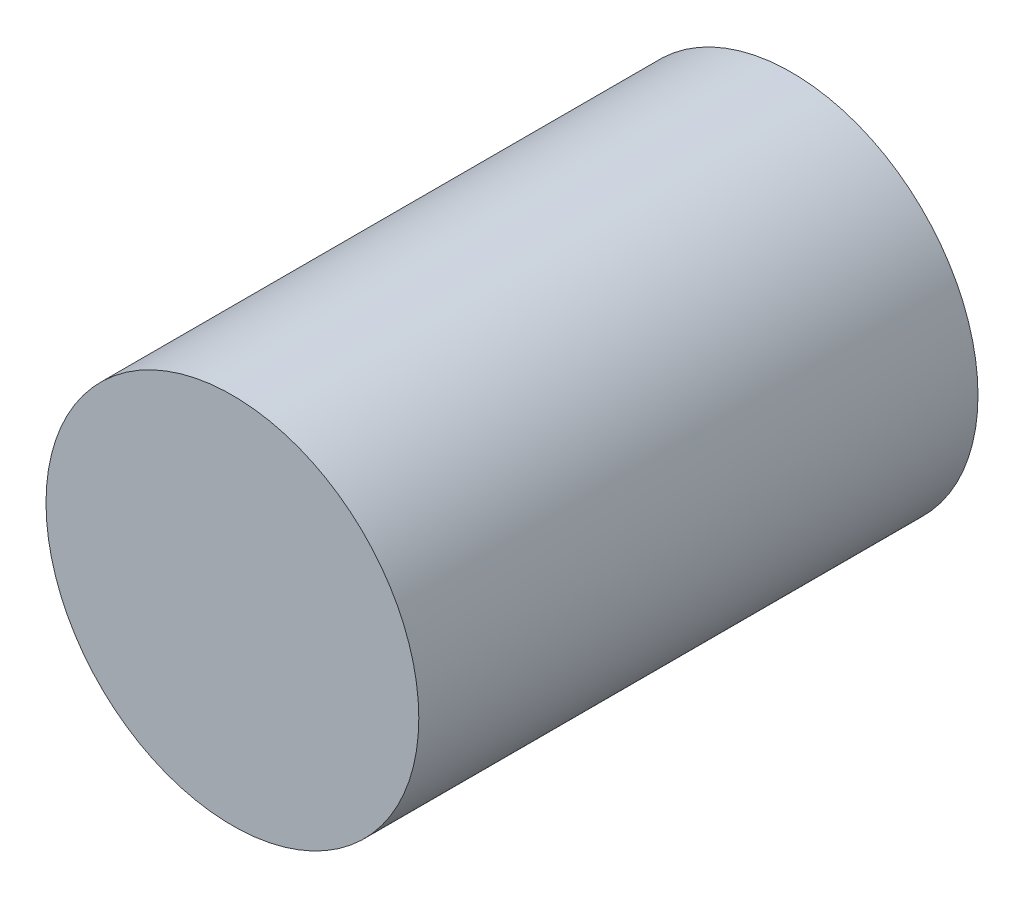
SolidWorks part; units mm, degrees
ref_plane "Front Plane" through (0, 0, 0) normal (0, 0, 1) x (1, 0, 0)
ref_plane "Top Plane" through (0, 0, 0) normal (0, 1, 0) x (1, 0, 0)
ref_plane "Right Plane" through (0, 0, 0) normal (1, 0, 0) x (0, 0, -1)
sketch "Sketch1" plane through (0, 0, 0) normal (0, 0, 1) x (1, 0, 0)
  circle A0 centre (-9.5269, 14.0102) radius 5.08
extrude "Boss-Extrude1" add sketch "Sketch1" along normal blind 15.24
